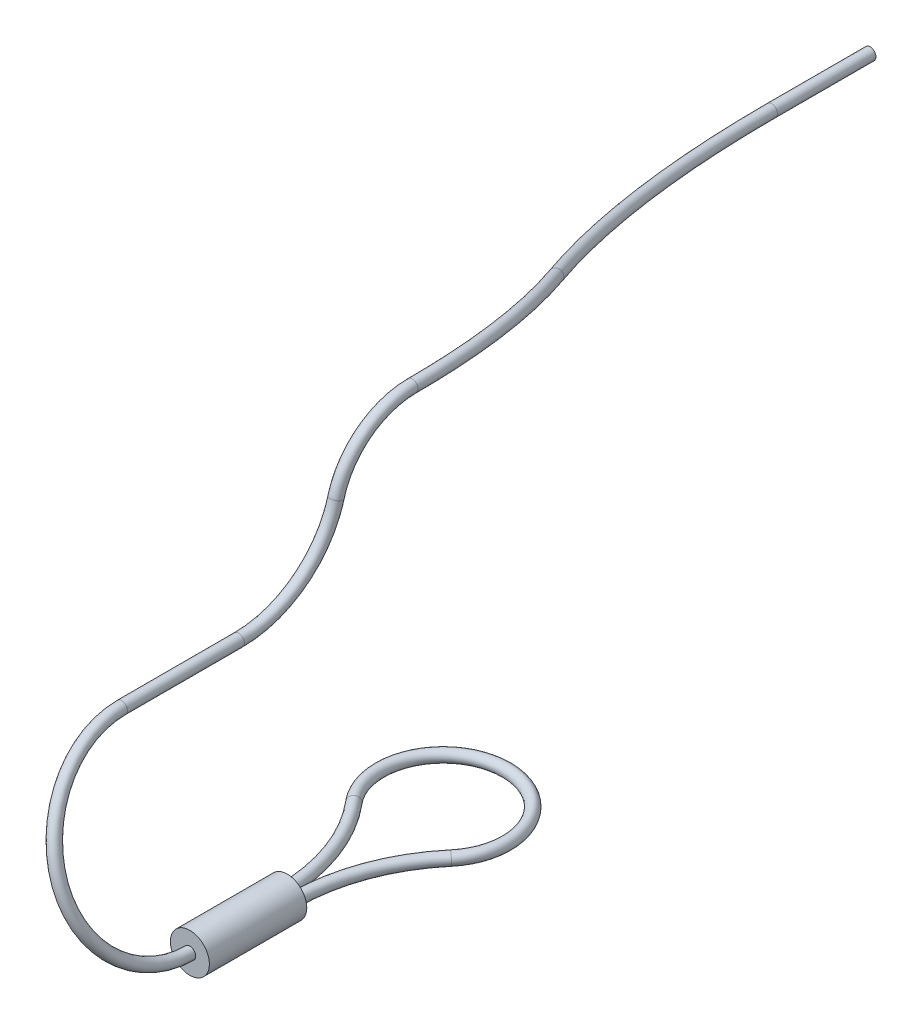
SolidWorks part; units mm, degrees
ref_plane "Front Plane" through (0, 0, 0) normal (0, 0, 1) x (1, 0, 0)
ref_plane "Top Plane" through (0, 0, 0) normal (0, 1, 0) x (1, 0, 0)
ref_plane "Right Plane" through (0, 0, 0) normal (1, 0, 0) x (0, 0, -1)
sketch "Sketch1" plane through (0, 0, 0) normal (0, 1, 0) x (1, 0, 0)
  line L0 (0, 0) -> (6.5, -3) construction
  dimension "D1" = 6.5
  dimension "D2" = 3
ref_plane "Plane1" through (0, -13, 0) normal (0, 1, 0) x (-1, 0, 0)
sketch "Sketch2" plane through (0, -13, 0) normal (0, 1, 0) x (-1, 0, 0)
  line L0 (-10.325, 9) -> (-10.325, 14) construction
  line L1 (-9.675, 9) -> (-9.675, 14) construction
  line L2 (-10, 1) -> (-10, 9) construction
  line L3 (-9.675, 9) -> (-10.325, 9) construction
  line L4 (-10, 9) -> (-10, 14) construction
  arc A0 (-12.4835, 3.0963) -> (-7.5165, 3.0963) centre (-10, 1) ccw
  arc A1 (-12.4835, 3.0963) -> (-10.325, 9) centre (-19.4777, 9) ccw
  arc A2 (-7.5165, 3.0963) -> (-9.675, 9) centre (-0.5223, 9) cw
  dimension "D2" = 5
  dimension "D4" = 3.25
  dimension "D1" = 0.65
  dimension "D3" = 8
  dimension "D5" = 1
  dimension "D6" = 10
ref_plane "Plane2" through (0, 0, 9) normal (0, 0, 1) x (1, 0, 0)
sketch "Sketch3" plane through (0, 0, 9) normal (0, 0, 1) x (1, 0, 0)
  circle A0 centre (10.325, -13) radius 0.3
  dimension "D1" = 0.6
sketch "Sketch4" plane through (0, 0, 9) normal (0, 0, 1) x (1, 0, 0)
  circle A0 centre (10, -13) radius 1
  dimension "D1" = 2
sweep "Sweep1" add profiles "Sketch3" path "Sketch2"
extrude "Extrude1" add sketch "Sketch4" along normal blind 5
ref_plane "Plane3" through (6.5, 0, 0) normal (1, 0, 0) x (0, 0, -1)
sketch "Sketch5" plane through (6.5, 0, 0) normal (1, 0, 0) x (0, 0, -1)
  line L0 (-3, 0) -> (-8, -18.6603) construction
  line L1 (-3, 0) -> (-8, 0) construction
  line L2 (-8, -3.8366) -> (-14, -3.8366)
  line L3 (0.9097, 3) -> (5.9097, 3) construction
  arc A0 (-3, 0) -> (0.9097, 3) centre (0.9097, -1.0476) cw
  arc A1 (-3, 0) -> (-8, -3.8366) centre (-8, 1.3397) cw
  dimension "D1" = 3
  dimension "D2" = 75
  dimension "D3" = 5
ref_plane "Plane4" through (4.3936, 1.6782, 0) normal (-0.9342, -0.3568, 0) x (0, 0, 1)
sketch "Sketch6" plane through (4.3936, 1.6782, 0) normal (-0.9342, -0.3568, 0) x (0, 0, 1)
  arc A0 (14, -15.7124) -> (14, -5.9034) centre (14, -10.8079) ccw
sketch "Sketch7" plane through (0, 0, 14) normal (0, 0, 1) x (1, 0, 0)
  circle A0 centre (10, -13) radius 0.3
  circle A1 centre (10.325, -13) radius 0.3 construction
sweep "Sweep2" add profiles "Sketch7" path "Sketch6"
sketch "Sketch8" plane through (0, 0, 14) normal (0, 0, -1) x (0.9966, -0.0824, 0)
  circle A1 centre (6.7941, 3.2879) radius 0.3
  circle A2 centre (6.7941, 3.2879) radius 0.3
  dimension "D1" = 0
sweep "Sweep3" add profiles "Sketch8" path "Sketch5"
ref_plane "Plane5" through (0, 0, 0) normal (-0.4191, 0.908, 0) x (-0.908, -0.4191, 0)
sketch "Sketch9" plane through (0, 0, 0) normal (-0.4191, 0.908, 0) x (-0.908, -0.4191, 0)
  line L0 (-1, -24.9505) -> (-1, -30)
  arc A0 (-7.1589, -0.9097) -> (-4.6953, -10.526) centre (12.8411, -0.9097) ccw
  arc A1 (-4.6953, -10.526) -> (-1, -24.9505) centre (-31, -24.9505) cw
  dimension "D1" = 20
  dimension "D2" = 30
  dimension "D3" = 1
  dimension "D4" = 30
sketch "Sketch10" plane through (0, 0, -0.9097) normal (0, 0, -1) x (-1, 0, 0)
  circle A1 centre (-6.5, 3) radius 0.3
  circle A2 centre (-6.5, 3) radius 0.3
  dimension "D1" = 0
sweep "Sweep4" add profiles "Sketch10" path "Sketch9"
